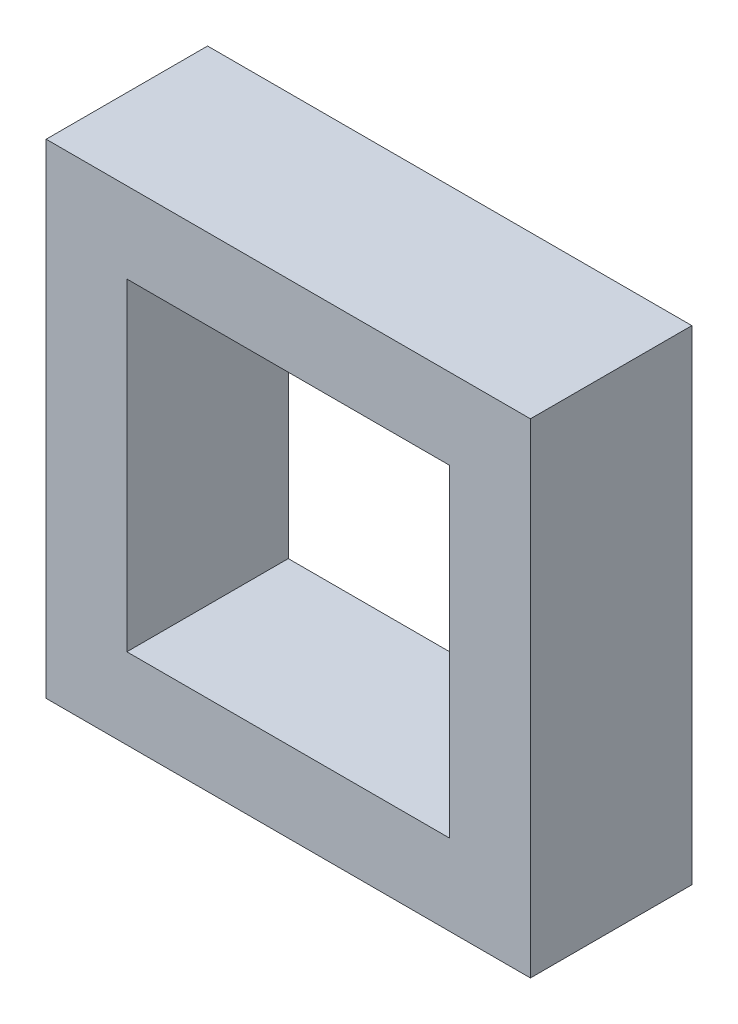
SolidWorks part; units mm, degrees
material "ABS"
ref_plane "Front Plane" through (0, 0, 0) normal (0, 0, 1) x (1, 0, 0)
ref_plane "Top Plane" through (0, 0, 0) normal (0, 1, 0) x (1, 0, 0)
ref_plane "Right Plane" through (0, 0, 0) normal (1, 0, 0) x (0, 0, -1)
sketch "Sketch1" plane through (0, 0, 0) normal (0, 0, 1) x (1, 0, 0)
  line L1 (0, 0) -> (4, 0)
  line L2 (0, 0) -> (0, 4)
  line L3 (0, 4) -> (4, 4)
  line L4 (4, 0) -> (4, 4)
  line L5 (5, 5) -> (-1, 5)
  line L6 (5, 5) -> (5, -1)
  line L7 (5, -1) -> (-1, -1)
  line L8 (-1, 5) -> (-1, -1)
  point P9 (2, 4)
  point P10 (2, 5)
  point P11 (4, 2)
  point P12 (5, 2)
  dimension "D1" = 6
  dimension "D2" = 6
  dimension "D3" = 4
  dimension "D4" = 4
extrude "Boss-Extrude1" add sketch "Sketch1" along normal blind 2
